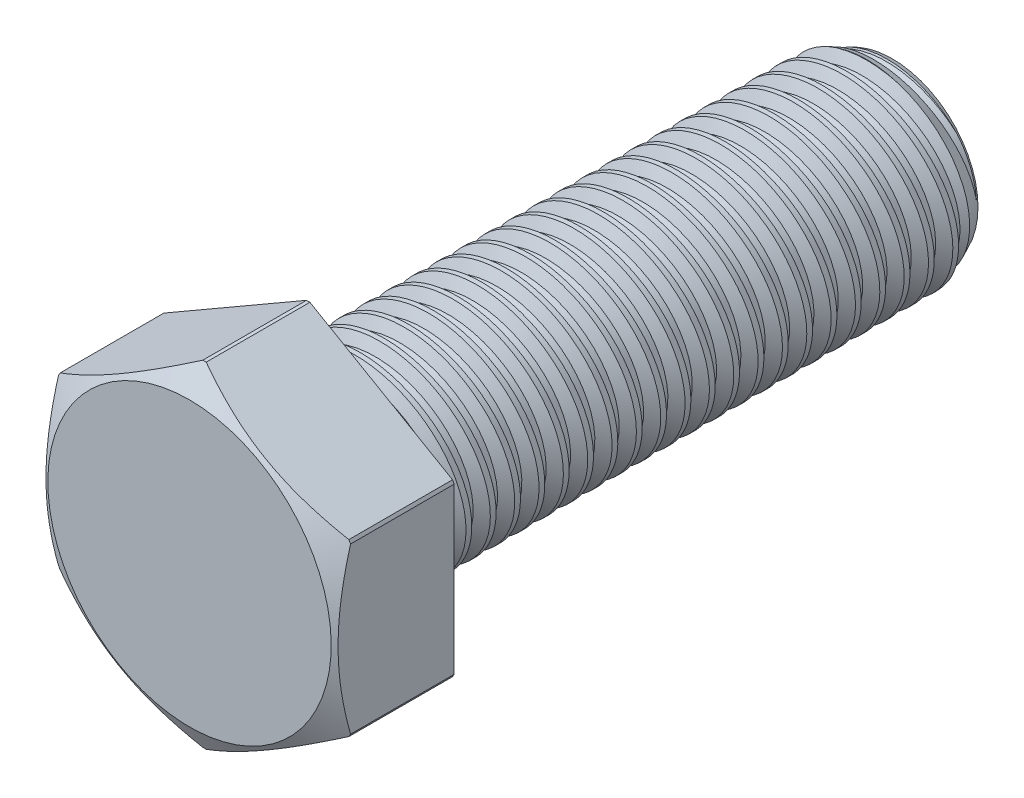
SolidWorks part; units mm, degrees
ref_plane "Front" through (0, 0, 0) normal (0, 0, 1) x (1, 0, 0)
ref_plane "Top" through (0, 0, 0) normal (0, 1, 0) x (1, 0, 0)
ref_plane "Right" through (0, 0, 0) normal (1, 0, 0) x (0, 0, -1)
sketch "Sketch1" plane through (0, 0, 0) normal (1, 0, 0) x (0, 0, -1)
  line L0 (-38.1, 0) -> (-53.5781, 0) construction
  line L1 (-38.1, 0) -> (-38.1, 19.05) construction
  line L2 (-38.1, 0) -> (-53.5781, 0) construction
  line L3 (-38.1, -12.7) -> (38.1, -12.7) construction
  line L4 (-38.1, 0) -> (38.1, 0)
  line L5 (-38.1, 0) -> (-38.1, 12.7)
  line L6 (-38.1, 12.7) -> (38.1, 12.7)
  line L7 (38.1, 0) -> (38.1, 12.7)
  dimension "Screw Dia" = 25.4
  dimension "Screw Length" = 76.2
  dimension "Head Height" = 15.4781
  dimension "Head Width" = 38.1
revolve "Revolve1" add sketch "Sketch1" angle 360 about L0
sketch "Sketch2" plane through (0, 0, 0) normal (1, 0, 0) x (0, 0, -1)
  line L0 (-38.1, 12.7) -> (-38.1, -12.7) construction
  line L1 (-38.1, -12.7) -> (-34.925, -12.7) construction
  line L2 (-34.925, -12.7) -> (-38.1, 12.7) construction
  line L3 (-38.1, 12.7) -> (-37.7062, 12.7492) construction
  line L4 (-34.9495, 13.0938) -> (-37.7062, 12.7492)
  line L5 (-37.7062, 12.7492) -> (-36.5085, 11.167)
  line L6 (-36.5085, 11.167) -> (-35.7209, 11.2655)
  line L7 (-35.7209, 11.2655) -> (-34.9495, 13.0938)
  line L8 (-36.1147, 11.2163) -> (-36.3279, 12.9215) construction
  line L9 (-38.1, 0) -> (-38.1, 12.7) construction
  line L10 (-38.1, 12.7) -> (-36.3002, 12.7) construction
  line L11 (-36.3002, 12.7) -> (-33.1252, -12.7) construction
  line L12 (-33.1252, -12.7) -> (-34.925, -12.7) construction
  line L13 (-38.1, -12.7) -> (38.1, -12.7) construction
  line L14 (-38.1, -0.4234) -> (-31.3253, 0.4234) construction
  line L15 (-38.1, 12.7) -> (38.1, 12.7) construction
  point P17 (-34.7127, 0)
  dimension "D1" = 3.175
  dimension "Thread Pitch" = 3.175
  dimension "D3" = 0.7937
  dimension "D4" = 0.3969
  dimension "D5" = 60
revolve "Cut-Revolve1" cut sketch "Sketch2" angle 360 about L14
sketch "Sketch3" plane through (0, 0, 0) normal (1, 0, 0) x (0, 0, -1)
  line L0 (34.8126, 12.7) -> (38.1, 11.167)
  line L1 (38.1, 11.167) -> (38.1, 12.7)
  line L2 (38.1, 12.7) -> (34.8126, 12.7)
  line L3 (-38.1, 12.7) -> (38.1, 12.7) construction
  line L4 (38.1, 0) -> (38.1, 12.7) construction
  line L5 (-36.5085, 11.167) -> (38.1, 11.167) construction
  line L6 (34.8126, 12.7) -> (34.8126, -12.7) construction
  line L7 (-38.1, -12.7) -> (38.1, -12.7) construction
  line L8 (0, 0) -> (34.8126, 0) construction
  dimension "D1" = 25
  dimension "D2" = 25.4
revolve "Cut-Revolve2" cut sketch "Sketch3" angle 360 about L8
pattern_linear "LPattern1" count 2 spacing 3.175 along (0, 0, 1) count 24 spacing 3.175 along (0, 0, 1)
sketch "Sketch5" plane through (0, 0, 38.1) normal (0, 0, 1) x (1, 0, 0)
  line L1 (0, 21.997) -> (-19.05, 10.9985)
  line L2 (-19.05, 10.9985) -> (-19.05, -10.9985)
  line L3 (-19.05, -10.9985) -> (0, -21.997)
  line L4 (0, -21.997) -> (19.05, -10.9985)
  line L5 (19.05, -10.9985) -> (19.05, 10.9985)
  line L6 (19.05, 10.9985) -> (0, 21.997)
  circle A0 centre (0, 0) radius 19.05 construction
  dimension "D1" = 38.1
extrude "Extrude1" add sketch "Sketch5" along normal up to vertex
sketch "Sketch6" plane through (0, 0, 0) normal (1, 0, 0) x (0, 0, -1)
  line L0 (-53.5781, 18.4785) -> (-51.62, 21.87)
  line L1 (-51.62, 21.87) -> (-38.1, 21.87)
  line L2 (-38.1, 21.87) -> (-38.1, 22.378)
  line L3 (-38.1, 22.378) -> (-53.5781, 22.378)
  line L4 (-53.5781, 22.378) -> (-53.5781, 18.4785)
  line L5 (-53.5781, 10.9985) -> (-53.5781, 21.997) construction
  line L6 (-53.5781, 21.997) -> (-38.1, 21.997) construction
  line L7 (-38.1, 10.9985) -> (-38.1, 21.997) construction
  line L8 (0, 0) -> (-51.62, 0) construction
  line L9 (-38.1, 0) -> (-53.5781, 0) construction
  line L10 (-51.62, 0) -> (-51.62, 21.87) construction
  line L11 (-45.8391, 22.378) -> (-45.8391, 0) construction
  dimension "D1" = 30
  dimension "D2" = 0.127
  dimension "D3" = 0.508
  dimension "D4" = 36.957
  dimension "D5" = 15.4781
  dimension "D6" = 76.2
revolve "Cut-Revolve3" cut sketch "Sketch6" angle 360 about L8
equation "\"D3@Sketch2\"=\"Thread Pitch@Sketch2\"/4"
equation "\"D4@Sketch2\"=\"Thread Pitch@Sketch2\"/8"
equation "\"D1@Sketch2\"=\"Thread Pitch@Sketch2\""
equation "\"D3@LPattern1\"=\"Thread Pitch@Sketch2\""
equation "\"D4@LPattern1\"=\"Thread Pitch@Sketch2\""
equation "\"D4@Sketch6\"=\"Head Width@Sketch1\"*.97"
equation "\"D2@LPattern1\"=\"Screw Length@Sketch1\"/\"Thread Pitch@Sketch2\""
